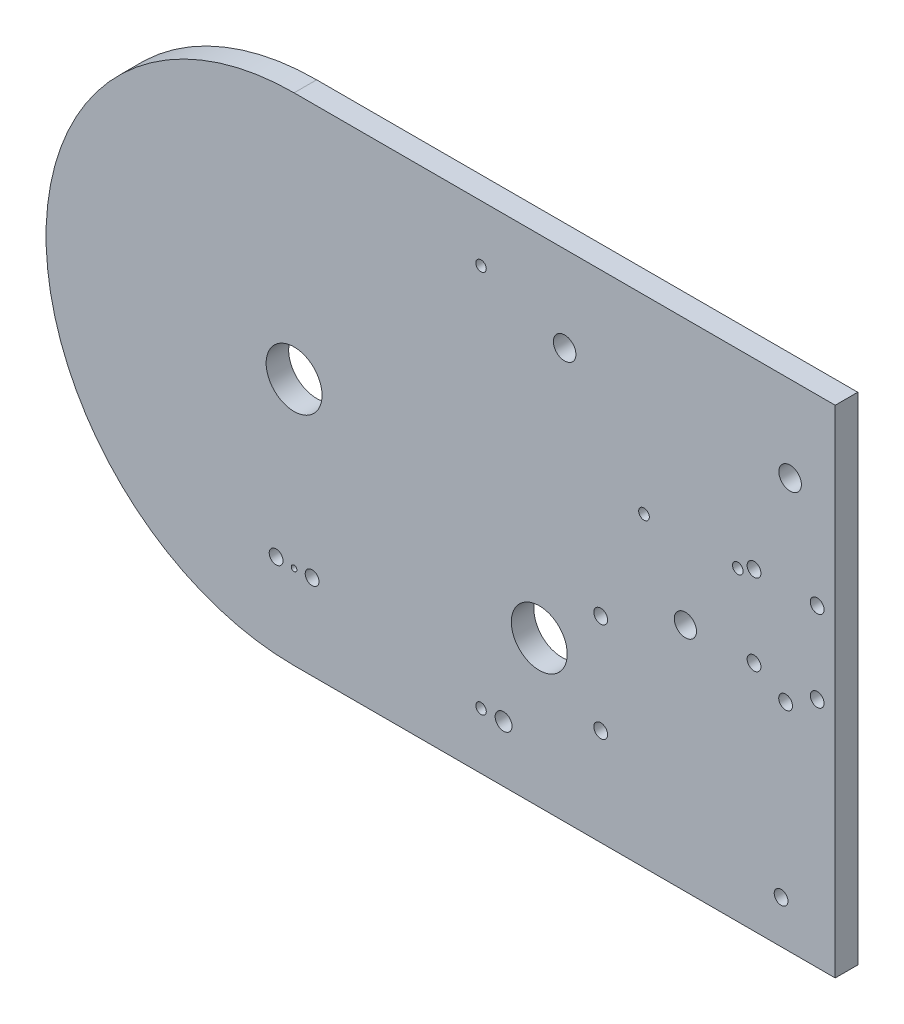
SolidWorks part; units mm, degrees
material "Acrylic (Medium-high impact)"
ref_plane "Front Plane" through (0, 0, 0) normal (0, 0, 1) x (1, 0, 0)
ref_plane "Top Plane" through (0, 0, 0) normal (0, 1, 0) x (1, 0, 0)
ref_plane "Right Plane" through (0, 0, 0) normal (1, 0, 0) x (0, 0, -1)
sketch "Sketch1" plane through (0, 0, 0) normal (0, 0, 1) x (1, 0, 0)
  line L0 (152.4, 69.85) -> (152.4, -69.85)
  line L3 (0, 65.098) -> (186.0446, 65.098) construction
  line L4 (0, -65.098) -> (195.2866, -65.098) construction
  line L5 (-66.2764, -69.85) -> (239.8849, -69.85) construction
  line L6 (0, 0) -> (93.3414, 0) construction
  line L7 (0, 69.85) -> (152.4, 69.85)
  line L8 (0, -69.85) -> (152.4, -69.85)
  circle A0 centre (0, 0) radius 67.6402 construction
  circle A2 centre (0, 0) radius 65.098 construction
  arc A3 (0, 69.85) -> (0, -69.85) centre (0, 0) ccw
  circle A5 centre (69.0541, -28.6031) radius 7.874
  circle A6 centre (0, 0) radius 7.874
  point P14 (46.6707, 0)
  dimension "D1" = 135.2804
  dimension "D2" = 130.1961
  dimension "D6" = 15.748
  dimension "D4" = 69.85
  dimension "D3" = 152.4
extrude "Boss-Extrude1" add sketch "Sketch1" along normal blind 6.35
sketch "Sketch2" plane through (0, 0, 6.35) normal (0, 0, 1) x (1, 0, 0)
  line L1 (152.4, -69.85) -> (152.4, 69.85) construction
  circle A0 centre (76.2, 45.72) radius 3.175
  circle A1 centre (139.7, 45.72) radius 3.175
  dimension "D2" = 6.35
  dimension "D3" = 63.5
  dimension "D4" = 12.7
  dimension "D5" = 45.72
extrude "Cut-Extrude1" cut sketch "Sketch2" against normal up to next
sketch "Sketch3" plane through (0, 0, 6.35) normal (0, 0, 1) x (1, 0, 0)
  circle A0 centre (116.3886, -24.8535) radius 7 construction
  circle A1 centre (116.3886, -24.8535) radius 7 construction
  circle A2 centre (126.4038, -25.8631) radius 1.6 construction
  circle A3 centre (126.4038, -25.8631) radius 1.6
  circle A4 centre (113.538, -34.5073) radius 1.6 construction
  circle A5 centre (99.6191, -27.6873) radius 1.6 construction
  circle A6 centre (98.5658, -12.2231) radius 1.6 construction
  circle A7 centre (111.4316, -3.5789) radius 1.6 construction
  circle A8 centre (125.3506, -10.3989) radius 1.6 construction
  circle A9 centre (113.538, -34.5073) radius 1.6
  circle A10 centre (99.6191, -27.6873) radius 1.6
  circle A11 centre (98.5658, -12.2231) radius 1.6
  circle A12 centre (111.4316, -3.5789) radius 1.6
  circle A13 centre (125.3506, -10.3989) radius 1.6
  circle A14 centre (116.3886, -24.8535) radius 3.175
  dimension "D1" = 6.35
extrude "Cut-Extrude2" [suppressed] cut sketch "Sketch3" against normal up to next
sketch "Sketch5" plane through (0, 0, 6.35) normal (0, 0, 1) x (1, 0, 0)
  line L0 (152.4, 69.85) -> (0, 69.85) construction
  line L1 (0, -69.85) -> (152.4, -69.85) construction
  circle A0 centre (50.8, -53.975) radius 1.5875
  circle A1 centre (50.8, 53.975) radius 1.5875
  circle A2 centre (83.0935, -58.8536) radius 1.5875
  circle A3 centre (109.4487, -0.1813) radius 1.5875
  circle A4 centre (114.0239, -70.394) radius 1.5875
  circle A5 centre (109.4487, -35.4367) radius 35.2554 construction
  circle A6 centre (109.4487, -35.4367) radius 17.25 construction
  circle A7 centre (117.184, -38.356) radius 22.225 construction
  arc A8 (56.2331, -23.6118) -> (55.976, -24.3306) centre (69.0541, -28.6031) ccw construction
  circle A9 centre (63.2844, -23.2471) radius 40.7458 construction
  dimension "D1" = 3.175
  dimension "D5" = 4.7625
  dimension "D7" = 228.379
  dimension "D6" = 4.7625
  dimension "D2" = 15.875
  dimension "D3" = 15.875
  dimension "D4" = 50.8
  dimension "D8" = 55.835
extrude "Cut-Extrude4" [suppressed] cut sketch "Sketch5" against normal up to next
sketch "Sketch7" plane through (0, 0, 6.35) normal (0, 0, 1) x (1, 0, 0)
  line L0 (152.4, -69.85) -> (152.4, 69.85) construction
  line L1 (152.4, 58.42) -> (38.1, 58.42) construction
  line L2 (152.4, 58.42) -> (152.4, 33.02) construction
  line L3 (152.4, 33.02) -> (38.1, 33.02) construction
  line L4 (38.1, 58.42) -> (38.1, 33.02) construction
  line L5 (69.0541, -69.85) -> (229.9837, 20.32)
  line L6 (0, -69.85) -> (152.4, -69.85) construction
  line L7 (69.0541, -69.85) -> (152.4, -69.85)
  line L8 (152.4, -69.85) -> (152.4, 20.32)
  line L9 (229.9837, 71.12) -> (152.4, 71.12)
  line L10 (229.9837, 71.12) -> (231.2582, 69.85)
  line L12 (229.9837, 20.32) -> (152.4, 20.32)
  line L13 (152.4, 71.12) -> (152.4, 69.85)
  line L14 (152.4, 69.85) -> (231.2582, 69.85)
  line L15 (152.4, 69.85) -> (0, 69.85) construction
  circle A1 centre (69.0541, -28.6031) radius 35.9834 construction
  point P6 (38.1, 45.72)
  point P7 (76.2, 45.72)
  dimension "D3" = 71.9668
  dimension "D1" = 25.4
  dimension "D2" = 114.3
  dimension "D4" = 12.7
  dimension "D5" = 12.7
  dimension "D6" = 330.738
  dimension "D7" = 135.1
extrude "Cut-Extrude5" [suppressed] cut sketch "Sketch7" against normal up to next
fillet "Fillet1" [suppressed] radius 25.4
sketch "Sketch8" plane through (0, 0, 6.35) normal (0, 0, 1) x (1, 0, 0)
  circle A11 centre (110.2068, -4.8436) radius 3.127
  arc A12 (112.9657, -6.0221) -> (109.848, -7.8221) centre (110.2068, -4.8436) ccw construction
  dimension "D1" = 0.127
extrude "Cut-Extrude6" cut sketch "Sketch8" against normal up to next
hole_wizard "#4 Clearance Hole1" positions "Sketch10" profile "Sketch9" hole size "#4" standard "Ansi Inch" end condition up to next
sketch "Sketch10" plane through (0, 0, 6.35) normal (0, 0, 1) x (1, 0, 0)
  line L0 (0, -69.85) -> (152.4, -69.85) construction
  line L1 (152.4, 69.85) -> (0, 69.85) construction
  circle A0 centre (0, 0) radius 75.4041 construction
  arc A1 (66.1989, 19.6512) -> (60.6967, 32.9298) centre (0, 0) ccw construction
  point P0 (52.6543, 53.975)
  point P4 (52.6543, -53.975)
  dimension "D1" = 6.35
  dimension "D2" = 15.875
  dimension "D3" = 15.875
sketch "Sketch9" plane through (52.6543, 53.975, 6.35) normal (1, 0, 0) x (0, -1, 0)
  line L0 (0, 0) -> (0, 6.35)
  line L1 (0, 6.35) -> (1.4732, 6.35)
  line L2 (1.4732, 6.35) -> (1.4732, 0)
  line L5 (1.4732, 0) -> (0, 0)
  line L11 (0, -6.35) -> (0, 107.95) construction
  dimension "Thru Hole Dia." = 2.9464
  dimension "Thru Hole Depth" = 6.35
hole_wizard "#4 Clearance Hole2" positions "Sketch12" profile "Sketch11" hole size "#4" standard "Ansi Inch" end condition up to next
sketch "Sketch12" plane through (0, 0, 6.35) normal (0, 0, 1) x (1, 0, 0)
  point P0 (129.54, 18.415)
  point P1 (147.32, 18.415)
  point P7 (147.32, -4.445)
  point P10 (129.54, -4.445)
  point P13 (138.43, -9.525)
  point P16 (86.36, -14.605)
  point P19 (86.36, -42.545)
  point P22 (137.16, -57.785)
  point P26 (5.0732, -45.873)
  point P30 (-5.0614, -45.873)
sketch "Sketch11" plane through (129.54, 18.415, 6.35) normal (1, 0, 0) x (0, -1, 0)
  line L0 (0, 0) -> (0, 6.35)
  line L1 (0, 6.35) -> (1.9431, 6.35)
  line L2 (1.9431, 6.35) -> (1.9431, 0)
  line L5 (1.9431, 0) -> (0, 0)
  line L11 (0, -6.35) -> (0, 107.95) construction
  dimension "Thru Hole Dia." = 3.8862
  dimension "Thru Hole Depth" = 6.35
sketch "Sketch13" plane through (0, 0, 6.35) normal (0, 0, 1) x (1, 0, 0)
  circle A0 centre (0.0059, -46.1405) radius 0.7937
  dimension "D1" = 1.5875
extrude "Cut-Extrude7" cut sketch "Sketch13" against normal up to next
sketch "Sketch14" plane through (0, 0, 6.35) normal (0, 0, 1) x (1, 0, 0)
  circle A0 centre (59.0043, -53.975) radius 2.3812
  dimension "D1" = 4.7625
  dimension "D2" = 6.35
extrude "Cut-Extrude8" cut sketch "Sketch14" against normal up to next
hole_wizard "#2 Clearance Hole1" positions "Sketch16" profile "Sketch15" hole size "#2" standard "Ansi Inch" end condition up to next
sketch "Sketch16" plane through (0, 0, 6.35) normal (0, 0, 1) x (1, 0, 0)
  circle A0 centre (98.552, 16.383) radius 1.1303 construction
  point P0 (98.552, 16.383)
  point P1 (124.968, 16.383)
sketch "Sketch15" plane through (98.552, 16.383, 6.35) normal (1, 0, 0) x (0, -1, 0)
  line L0 (0, 0) -> (0, 6.35)
  line L1 (0, 6.35) -> (1.4986, 6.35)
  line L2 (1.4986, 6.35) -> (1.4986, 0)
  line L5 (1.4986, 0) -> (0, 0)
  line L11 (0, -6.35) -> (0, 107.95) construction
  dimension "Thru Hole Dia." = 2.9972
  dimension "Thru Hole Depth" = 6.35
